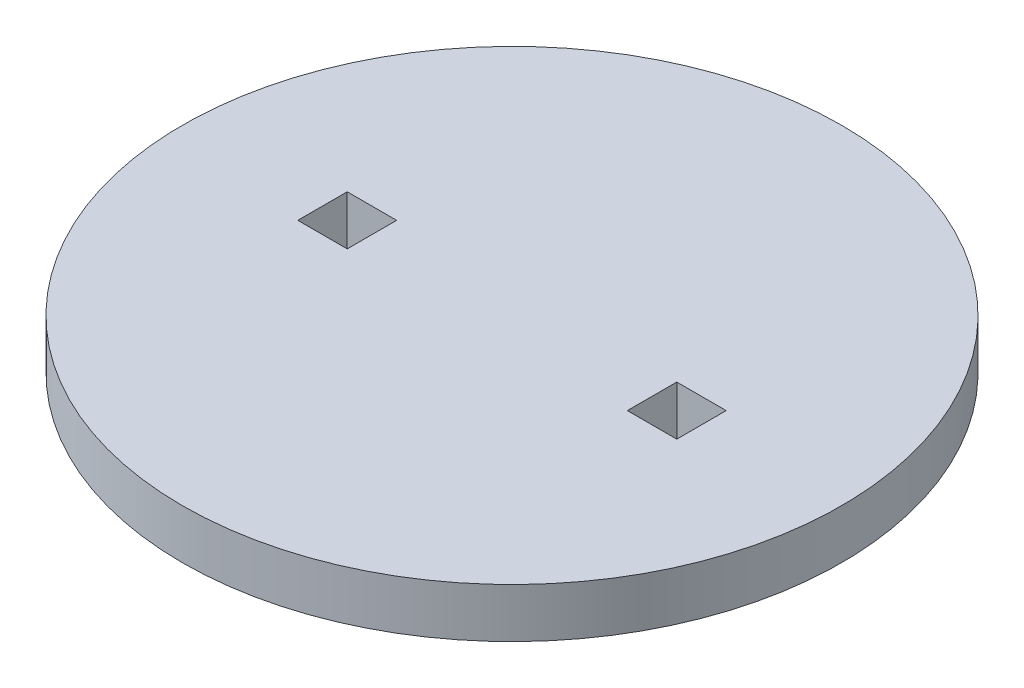
SolidWorks part; units mm, degrees
ref_plane "Alzado" through (0, 0, 0) normal (0, 0, 1) x (1, 0, 0)
ref_plane "Planta" through (0, 0, 0) normal (0, 1, 0) x (1, 0, 0)
ref_plane "Vista lateral" through (0, 0, 0) normal (1, 0, 0) x (0, 0, -1)
sketch "Croquis1" plane through (0, 0, 0) normal (0, 1, 0) x (1, 0, 0)
  line L0 (0, 40) -> (0, -40) construction
  line L1 (-23, 3) -> (-17, 3)
  line L2 (-23, 3) -> (-23, -3)
  line L3 (-23, -3) -> (-17, -3)
  line L4 (-17, 3) -> (-17, -3)
  line L5 (-23, 3) -> (-17, -3) construction
  line L6 (-23, -3) -> (-17, 3) construction
  line L7 (23, -3) -> (17, 3) construction
  line L8 (23, 3) -> (17, -3) construction
  line L9 (17, 3) -> (17, -3)
  line L10 (23, -3) -> (17, -3)
  line L11 (23, 3) -> (23, -3)
  line L12 (23, 3) -> (17, 3)
  circle A0 centre (0, 0) radius 40
  point P3 (-20, 0)
  point P15 (20, 0)
  dimension "D1" = 80
  dimension "D2" = 6
  dimension "D3" = 6
  dimension "D4" = 20
extrude "Saliente-Extruir1" add sketch "Croquis1" along normal blind 6
